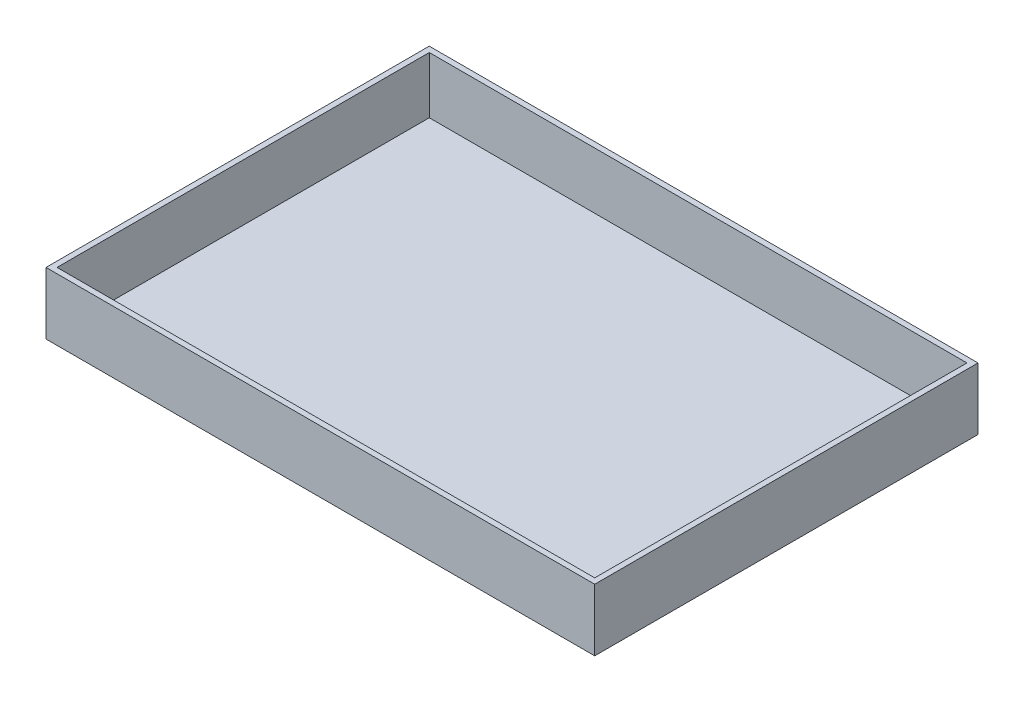
SolidWorks part; units mm, degrees
material "ABS"
ref_plane "Front Plane" through (0, 0, 0) normal (0, 0, 1) x (1, 0, 0)
ref_plane "Top Plane" through (0, 0, 0) normal (0, 1, 0) x (1, 0, 0)
ref_plane "Right Plane" through (0, 0, 0) normal (1, 0, 0) x (0, 0, -1)
sketch "Sketch1" plane through (0, 0, 0) normal (0, 1, 0) x (1, 0, 0)
  line L1 (0, 0) -> (252.73, 0)
  line L2 (0, 0) -> (0, -176.53)
  line L3 (0, -176.53) -> (252.73, -176.53)
  line L4 (252.73, 0) -> (252.73, -176.53)
extrude "Boss-Extrude1" add sketch "Sketch1" along normal blind 28.575
shell "Shell1" thickness 2.54
